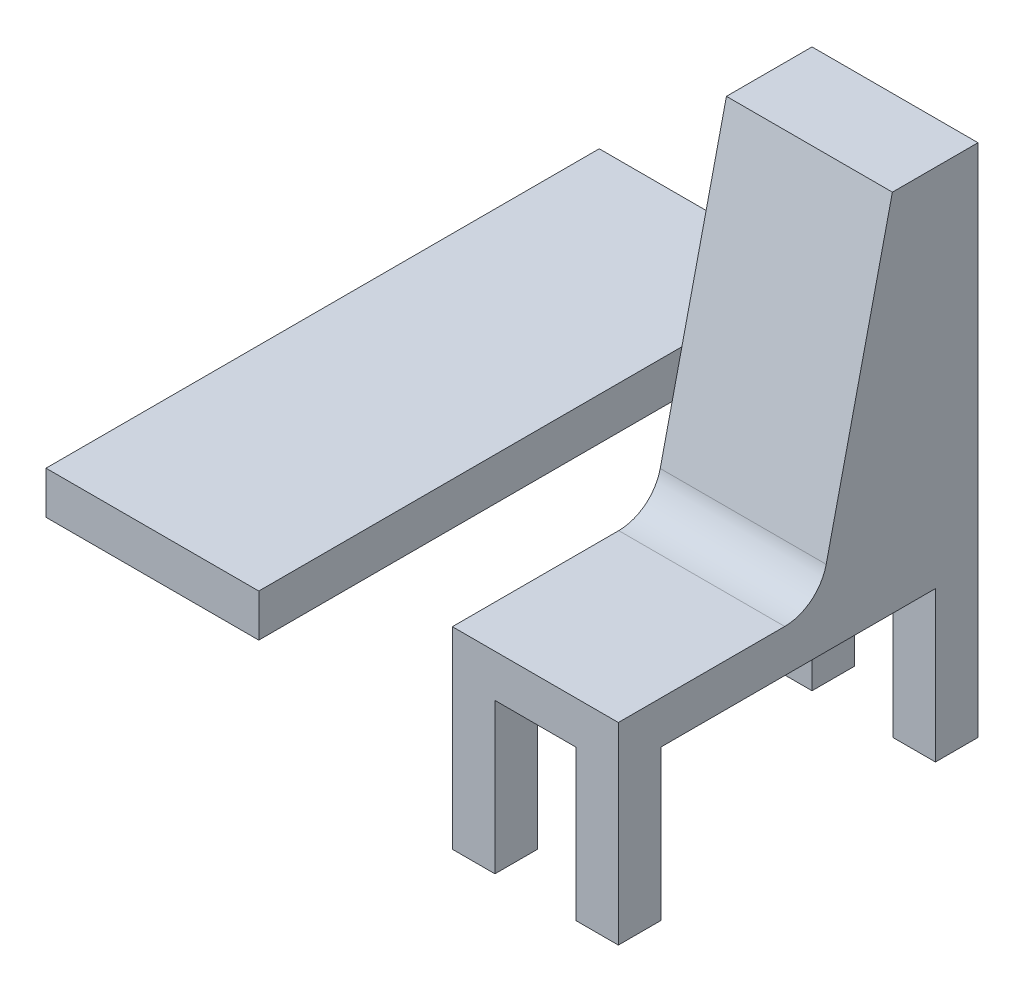
SolidWorks part; units mm, degrees
ref_plane "Front Plane" through (0, 0, 0) normal (0, 0, 1) x (1, 0, 0)
ref_plane "Top Plane" through (0, 0, 0) normal (0, 1, 0) x (1, 0, 0)
ref_plane "Right Plane" through (0, 0, 0) normal (1, 0, 0) x (0, 0, -1)
sketch "Sketch1" plane through (0, 0, 0) normal (1, 0, 0) x (0, 0, -1)
  line L0 (254.379, 460.6789) -> (81.0729, -296.6179)
  line L1 (81.0729, -296.6179) -> (-389.5499, -296.6179)
  line L2 (-389.5499, -296.6179) -> (-389.5499, -749.6196)
  line L3 (-389.5499, -749.6196) -> (455.5435, -749.6196)
  line L4 (455.5435, -749.6196) -> (455.5435, 460.6789)
  line L5 (455.5435, 460.6789) -> (254.379, 460.6789)
  arc A0 (-430.2589, -294.9686) -> (23.9321, -266.9138) centre (-327.6512, 1734.4391) ccw construction
  arc A1 (-455.7644, -629.8731) -> (-383.1646, -236.2927) centre (-2583.6741, -33.8728) ccw construction
  point P2 (82.7521, -314.6822)
  point P7 (0, 0)
  point P8 (-389.5499, -296.6179)
extrude "Boss-Extrude1" add sketch "Sketch1" along normal mid plane 390
sketch "Sketch2" plane through (-195, 0, 0) normal (-1, 0, 0) x (0, 0, 1)
  line L0 (389.5499, -749.6196) -> (-455.5435, -749.6196) construction
  line L1 (-355.5435, -749.6196) -> (289.5499, -749.6196)
  line L2 (-355.5435, -749.6196) -> (-355.5435, -396.6179)
  line L3 (-355.5435, -396.6179) -> (289.5499, -396.6179)
  line L4 (289.5499, -749.6196) -> (289.5499, -396.6179)
  line L5 (289.5499, -396.6179) -> (289.5499, -296.6179) construction
  line L6 (-81.0729, -296.6179) -> (389.5499, -296.6179) construction
  line L7 (289.5499, -573.1188) -> (389.5499, -573.1188) construction
  line L8 (389.5499, -296.6179) -> (389.5499, -749.6196) construction
  line L9 (-355.5435, -573.1188) -> (-455.5435, -573.1188) construction
  line L10 (-455.5435, -749.6196) -> (-455.5435, 460.6789) construction
  dimension "D1" = 100
extrude "Cut-Extrude1" cut sketch "Sketch2" against normal through all both and the other way through all
fillet "Fillet1" radius 100 1 edges at (0, -296.6179, -81.0729)
sketch "Sketch3" plane through (0, 0, -455.5435) normal (0, 0, -1) x (-1, 0, 0)
  line L0 (0, 0) -> (0, -749.6196) construction
  line L1 (-195, -749.6196) -> (195, -749.6196) construction
  line L2 (195, -749.6196) -> (195, 460.6789) construction
  line L3 (-95, -749.6196) -> (95, -749.6196)
  line L4 (-95, -749.6196) -> (-95, -396.6179)
  line L5 (-95, -396.6179) -> (95, -396.6179)
  line L6 (95, -749.6196) -> (95, -396.6179)
  line L7 (-95, -749.6196) -> (95, -396.6179) construction
  line L8 (-95, -396.6179) -> (95, -749.6196) construction
  line L9 (-195, -396.6179) -> (195, -396.6179) construction
  point P5 (0, -573.1188)
  point P10 (96.5041, -452.9806)
  dimension "D1" = 100
extrude "Cut-Extrude2" cut sketch "Sketch3" against normal through all both and the other way through all
sketch "Sketch4" plane through (-195, 0, 0) normal (-1, 0, 0) x (0, 0, 1)
  line L0 (-455.5435, 3.3821) -> (844.4565, 3.3821)
  line L1 (-455.5435, -749.6196) -> (-455.5435, 460.6789) construction
  line L2 (844.4565, 3.3821) -> (844.4565, -96.6179)
  line L3 (844.4565, -96.6179) -> (-455.5435, -96.6179)
  line L7 (-455.5435, -96.6179) -> (-455.5435, 3.3821)
  line L8 (-355.5435, -396.6179) -> (289.5499, -396.6179) construction
  dimension "D1" = 100
  dimension "D2" = 400
  dimension "D3" = 1300
extrude "Boss-Extrude2" add sketch "Sketch4" along normal blind 500
